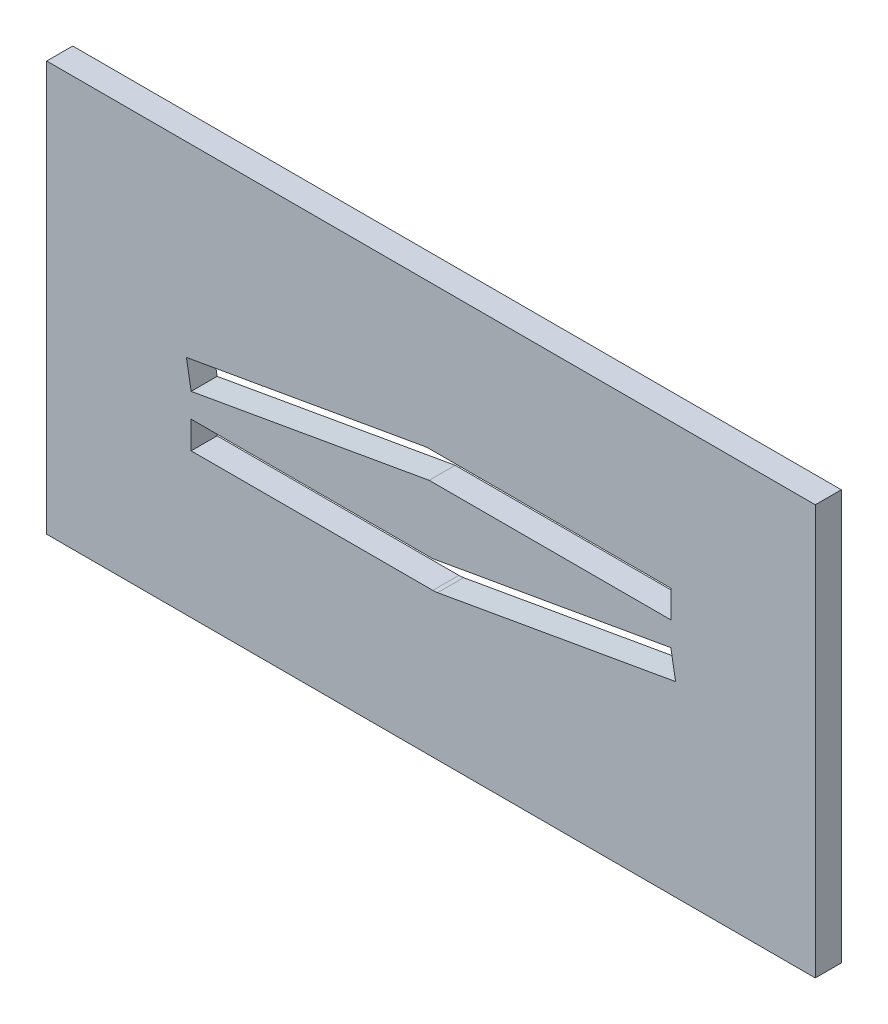
SolidWorks part; units mm, degrees
ref_plane "Front" through (0, 0, 0) normal (0, 0, 1) x (1, 0, 0)
ref_plane "Top" through (0, 0, 0) normal (0, 1, 0) x (1, 0, 0)
ref_plane "Right" through (0, 0, 0) normal (1, 0, 0) x (0, 0, -1)
sketch "Sketch1" plane through (0, 0, 0) normal (0, 0, 1) x (1, 0, 0)
  line L0 (-24.9049, -0.9289) -> (-0.1906, 3.4289)
  line L1 (-39.9049, 21.2789) -> (39.9049, 21.2789)
  line L2 (-39.9049, 21.2789) -> (-39.9049, -21.2789)
  line L3 (-39.9049, -21.2789) -> (39.9049, -21.2789)
  line L4 (39.9049, 21.2789) -> (39.9049, -21.2789)
  line L5 (-24.9049, -6.2789) -> (-24.9049, -21.2789) construction
  line L6 (-0.1906, 3.4289) -> (-0.6855, 6.2356) construction
  line L7 (-25.3998, 1.8778) -> (-0.6855, 6.2356)
  line L8 (-24.9049, -3.4289) -> (0.1906, -3.4289)
  line L9 (-24.9049, -6.2789) -> (-39.9049, -6.2789) construction
  line L10 (0.1906, -3.4289) -> (0.1906, -6.2789) construction
  line L11 (-24.9049, -6.2789) -> (0.1906, -6.2789)
  line L12 (-0.1906, 3.4289) -> (24.9049, 3.4289)
  line L13 (-24.9049, -2.1789) -> (24.9049, 2.1789) construction
  line L14 (-0.1906, 3.4289) -> (-0.1906, 6.2789) construction
  line L15 (24.9049, 3.4289) -> (24.9049, 6.2789)
  line L16 (-0.1906, 6.2789) -> (24.9049, 6.2789)
  line L17 (0.1906, -3.4289) -> (24.9049, 0.9289)
  line L18 (0.1906, -3.4289) -> (0.6855, -6.2356) construction
  line L19 (24.9049, 0.9289) -> (25.3998, -1.8778)
  line L20 (0.6855, -6.2356) -> (25.3998, -1.8778)
  line L21 (24.9049, 3.4289) -> (24.9049, 0.9289) construction
  line L22 (-0.6855, 6.2356) -> (-0.1906, 6.2789)
  line L23 (-0.1906, 3.4289) -> (0.1906, -3.4289) construction
  line L24 (0.1906, -6.2789) -> (0.6855, -6.2356)
  line L25 (-24.9049, -0.9289) -> (-24.9049, -3.4289) construction
  line L26 (-24.9049, -0.9289) -> (-25.3998, 1.8778)
  line L27 (-24.9049, -3.4289) -> (-24.9049, -6.2789)
  point P4 (0, 0)
  point P5 (0, 21.2789)
  point P7 (-39.9049, 0)
  point P16 (0, 0)
  dimension "D6" = 10
  dimension "D1" = 2.5
  dimension "D2" = 50
  dimension "D3" = 10
  dimension "D4" = 2.85
  dimension "D5" = 15
extrude "Boss-Extrude1" add sketch "Sketch1" along normal blind 2.7
sketch "Sketch2" [suppressed] plane through (0, 0, 2.7) normal (0, 0, 1) x (1, 0, 0)
  line L0 (32.4049, -13.6289) -> (39.9049, -13.6289) construction
  line L1 (39.9049, -21.1289) -> (39.9049, 21.1289) construction
  line L2 (32.4049, -13.6289) -> (32.4049, -21.1289) construction
  line L3 (-39.9049, -21.1289) -> (39.9049, -21.1289) construction
  line L4 (-32.4049, 13.6289) -> (-39.9049, 13.6289) construction
  line L5 (-39.9049, 21.1289) -> (-39.9049, -21.1289) construction
  line L6 (-32.4049, 13.6289) -> (-32.4049, 21.1289) construction
  line L7 (39.9049, 21.1289) -> (-39.9049, 21.1289) construction
  line L8 (-32.4049, -13.6289) -> (-39.9049, -13.6289) construction
  line L9 (-32.4049, -13.6289) -> (-32.4049, -21.1289) construction
  line L10 (32.4049, 13.6289) -> (39.9049, 13.6289) construction
  line L11 (32.4049, 13.6289) -> (32.4049, 21.1289) construction
  circle A0 centre (-32.4049, 13.6289) radius 3.25
  circle A1 centre (32.4049, -13.6289) radius 3.25
  circle A2 centre (32.4049, 13.6289) radius 3.25
  circle A3 centre (-32.4049, -13.6289) radius 3.25
  dimension "D1" = 6.5
  dimension "D2" = 7.5
extrude "Cut-Extrude1" [suppressed] cut sketch "Sketch2" against normal blind 10
sketch "Sketch3" [suppressed] plane through (0, 0, 2.7) normal (0, 0, 1) x (1, 0, 0)
  line L4 (-24.9049, -3.4289) -> (-24.9049, -0.9289)
  line L5 (-24.9049, -0.9289) -> (-0.1906, 3.4289)
  line L6 (-0.1906, 3.4289) -> (24.9049, 3.4289)
  line L7 (24.9049, 3.4289) -> (24.9049, 0.9289)
  line L8 (24.9049, 0.9289) -> (0.1906, -3.4289)
  line L9 (0.1906, -3.4289) -> (-24.9049, -3.4289)
sketch "Sketch4" [suppressed] plane through (0, 0, 2.7) normal (0, 0, 1) x (1, 0, 0)
  line L0 (-24.9049, -0.9289) -> (-25.3737, 1.7301)
  line L1 (-25.3737, 1.7301) -> (-0.6595, 6.0879)
  line L2 (-0.6595, 6.0879) -> (-0.1906, 6.1289)
  line L3 (-0.1906, 6.1289) -> (24.9049, 6.1289)
  line L4 (24.9049, 6.1289) -> (24.9049, 3.4289)
  line L5 (24.9049, 3.4289) -> (-0.1906, 3.4289)
  line L6 (-0.1906, 3.4289) -> (-24.9049, -0.9289)
  line L8 (-24.9049, -6.1289) -> (-24.9049, -3.4289)
  line L9 (-24.9049, -3.4289) -> (0.1906, -3.4289)
  line L10 (0.1906, -3.4289) -> (24.9049, 0.9289)
  line L11 (24.9049, 0.9289) -> (25.3737, -1.7301)
  line L12 (25.3737, -1.7301) -> (0.6595, -6.0879)
  line L13 (0.6595, -6.0879) -> (0.1906, -6.1289)
  line L14 (0.1906, -6.1289) -> (-24.9049, -6.1289)
extrude "Boss-Extrude2" [suppressed] add sketch "Sketch4" against normal up to surface (2.7 mm away)
extrude "Cut-Extrude2" [suppressed] cut sketch "Sketch3" against normal blind 10
sketch "Sketch5" [suppressed] plane through (0, 0, 2.7) normal (0, 0, 1) x (1, 0, 0)
  line L0 (-19.9581, -2.9961) -> (-19.9581, -0.4961)
  line L3 (-19.9581, -0.4961) -> (-0.1528, 2.9961)
  line L4 (-0.1528, 2.9961) -> (19.9581, 2.9961)
  line L5 (19.9581, 2.9961) -> (19.9581, 0.4961)
  line L7 (19.9581, 0.4961) -> (0.1528, -2.9961)
  line L9 (0.1528, -2.9961) -> (-19.9581, -2.9961)
extrude "Cut-Extrude3" [suppressed] cut sketch "Sketch5" against normal blind 22.7
sketch "Sketch6" [suppressed] plane through (0, 0, 2.7) normal (0, 0, 1) x (1, 0, 0)
  line L0 (-22.1849, -3.4289) -> (-22.4428, -0.4948)
  line L1 (0.1906, -3.4289) -> (-24.9049, -3.4289) construction
  line L2 (-24.9049, -0.9289) -> (-0.1906, 3.4289) construction
  line L3 (-22.4428, -0.4948) -> (-0.1906, 3.4289)
  line L4 (-0.1906, 3.4289) -> (22.1849, 3.4289)
  line L5 (-0.1906, 3.4289) -> (24.9049, 3.4289) construction
  line L6 (22.1849, 3.4289) -> (22.4428, 0.4948)
  line L7 (24.9049, 0.9289) -> (0.1906, -3.4289) construction
  line L8 (22.4428, 0.4948) -> (0.1906, -3.4289)
  line L9 (0.1906, -3.4289) -> (-22.1849, -3.4289)
  line L10 (-22.3139, -1.9618) -> (22.3139, 1.9618) construction
  dimension "D1" = 2.5
extrude "Cut-Extrude4" [suppressed] cut sketch "Sketch6" against normal blind 10
